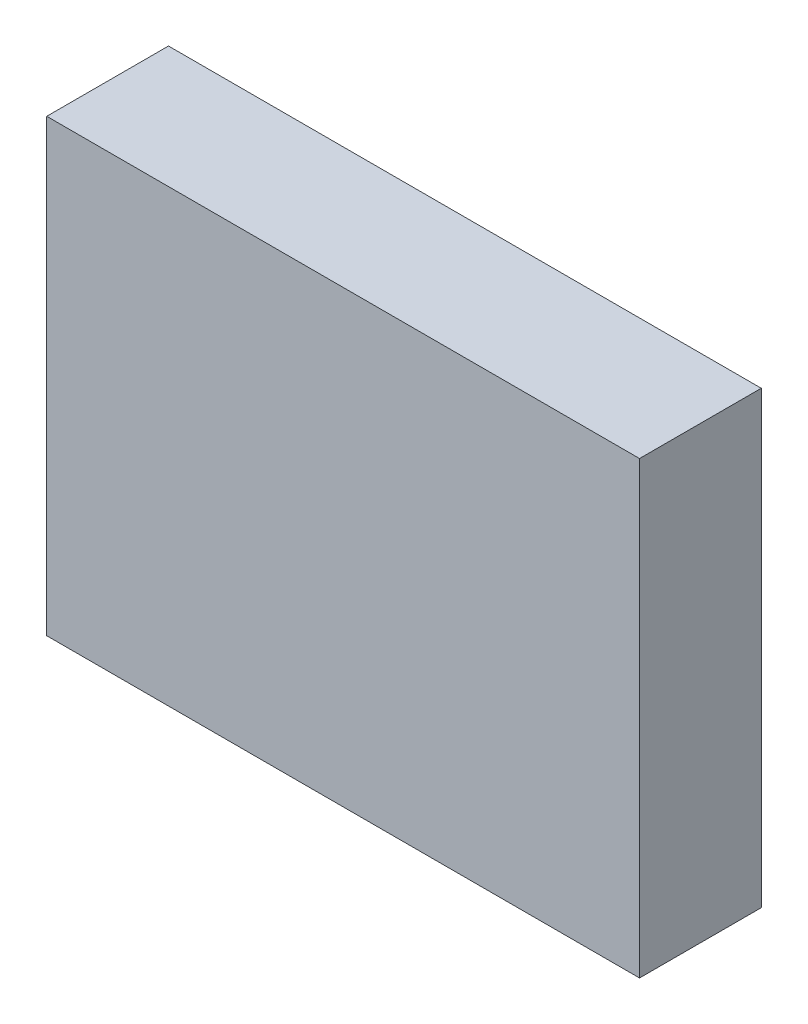
SolidWorks part; units mm, degrees
ref_plane "Front Plane" through (0, 0, 0) normal (0, 0, 1) x (1, 0, 0)
ref_plane "Top Plane" through (0, 0, 0) normal (0, 1, 0) x (1, 0, 0)
ref_plane "Right Plane" through (0, 0, 0) normal (1, 0, 0) x (0, 0, -1)
sketch "Sketch1" plane through (0, 0, 0) normal (0, 0, 1) x (1, 0, 0)
  line L1 (0, 0) -> (22.4, 0)
  line L2 (0, 0) -> (0, 17)
  line L3 (0, 17) -> (22.4, 17)
  line L4 (22.4, 0) -> (22.4, 17)
  dimension "D1" = 17
  dimension "D2" = 22.4
extrude "Boss-Extrude1" add sketch "Sketch1" along normal blind 4.6
